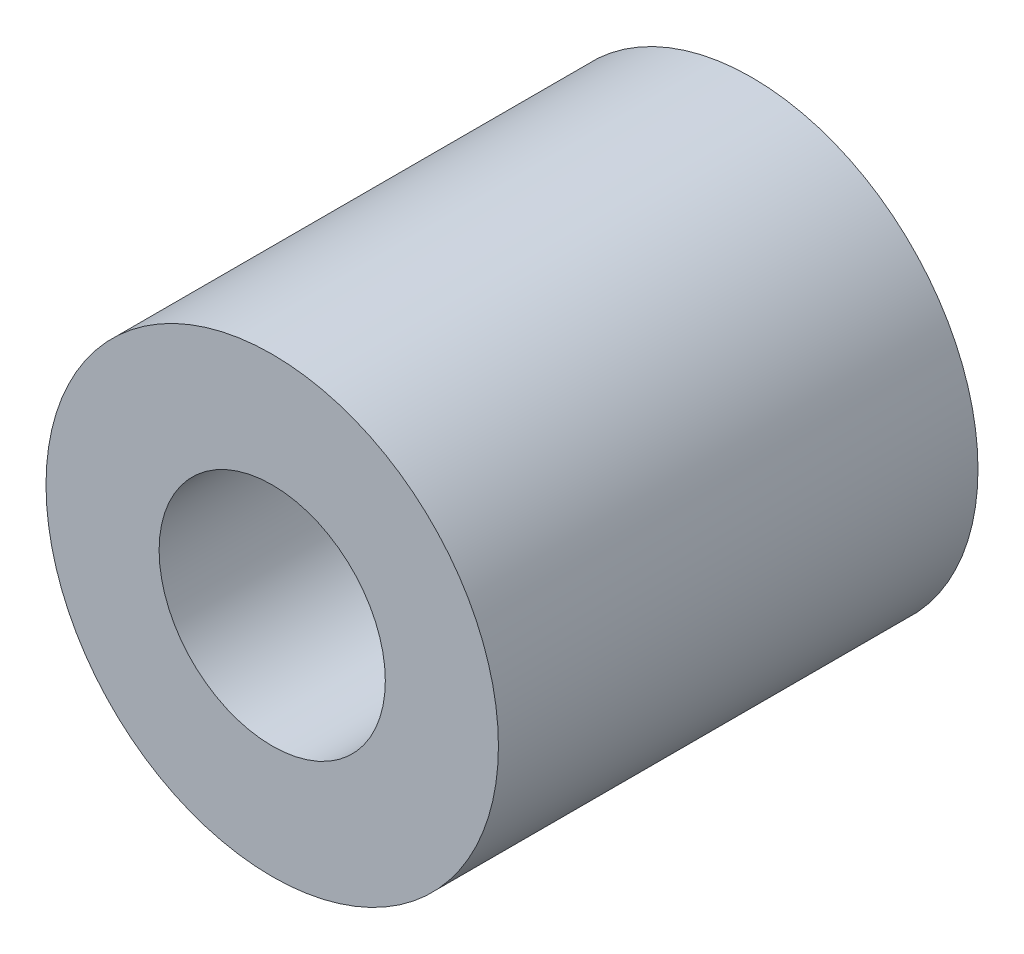
SolidWorks part; units mm, degrees
ref_plane "Front Plane" through (0, 0, 0) normal (0, 0, 1) x (1, 0, 0)
ref_plane "Top Plane" through (0, 0, 0) normal (0, 1, 0) x (1, 0, 0)
ref_plane "Right Plane" through (0, 0, 0) normal (1, 0, 0) x (0, 0, -1)
sketch "Sketch1" plane through (0, 0, 0) normal (0, 0, 1) x (1, 0, 0)
  circle A0 centre (0, 0) radius 5
  dimension "D1" = 10
extrude "Boss-Extrude1" add sketch "Sketch1" along normal blind 10.6
hole_wizard "Ø5.0mm Dowel Hole1" positions "Sketch2" profile "Sketch3" hole size "Ø5.0" standard "ANSI Metric" end condition up to next
sketch "Sketch2" plane through (0, 0, 10.6) normal (0, 0, 1) x (1, 0, 0)
  point P0 (0, 0)
sketch "Sketch3" plane through (0, 0, 10.6) normal (1, 0, 0) x (0, -1, 0)
  line L0 (0, 0) -> (0, 10.6)
  line L1 (0, 10.6) -> (2.5, 10.6)
  line L2 (2.5, 10.6) -> (2.5, 0)
  line L5 (2.5, 0) -> (0, 0)
  line L11 (0, -6.35) -> (0, 107.95) construction
  dimension "Thru Hole Dia." = 5
  dimension "Thru Hole Depth" = 10.6
